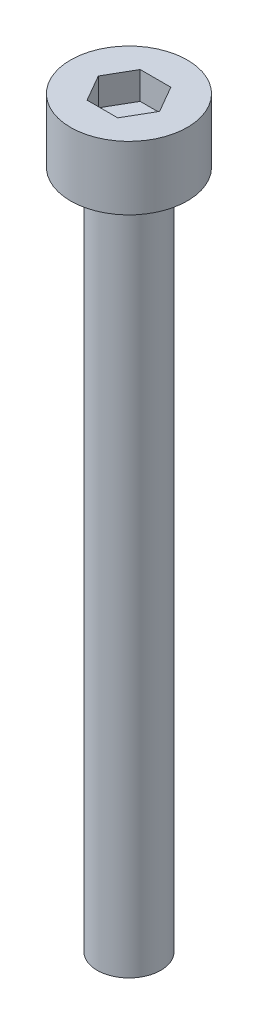
SolidWorks part; units mm, degrees
material "AISI 304"
ref_plane "前视基准面" through (0, 0, 0) normal (0, 0, 1) x (1, 0, 0)
ref_plane "上视基准面" through (0, 0, 0) normal (0, 1, 0) x (1, 0, 0)
ref_plane "右视基准面" through (0, 0, 0) normal (1, 0, 0) x (0, 0, -1)
sketch "草图1" plane through (0, 0, 0) normal (0, 1, 0) x (1, 0, 0)
  circle A0 centre (0, 0) radius 2.75
  dimension "D1" = 5.5
extrude "杯头" add sketch "草图1" along normal blind 3
sketch "草图2" plane through (0, 3, 0) normal (0, 1, 0) x (1, 0, 0)
  line L1 (1.4434, 0) -> (0.7217, 1.25)
  line L2 (0.7217, 1.25) -> (-0.7217, 1.25)
  line L3 (-0.7217, 1.25) -> (-1.4434, 0)
  line L4 (-1.4434, 0) -> (-0.7217, -1.25)
  line L5 (-0.7217, -1.25) -> (0.7217, -1.25)
  line L6 (0.7217, -1.25) -> (1.4434, 0)
  circle A0 centre (0, 0) radius 1.25 construction
  dimension "D1" = 2.5
extrude "内六角口" cut sketch "草图2" against normal blind 1.3
sketch "草图3" plane through (0, 0, 0) normal (0, -1, 0) x (1, 0, 0)
  circle A0 centre (0, 0) radius 1.5
  dimension "D1" = 3
extrude "螺纹长" add sketch "草图3" along normal blind 32
